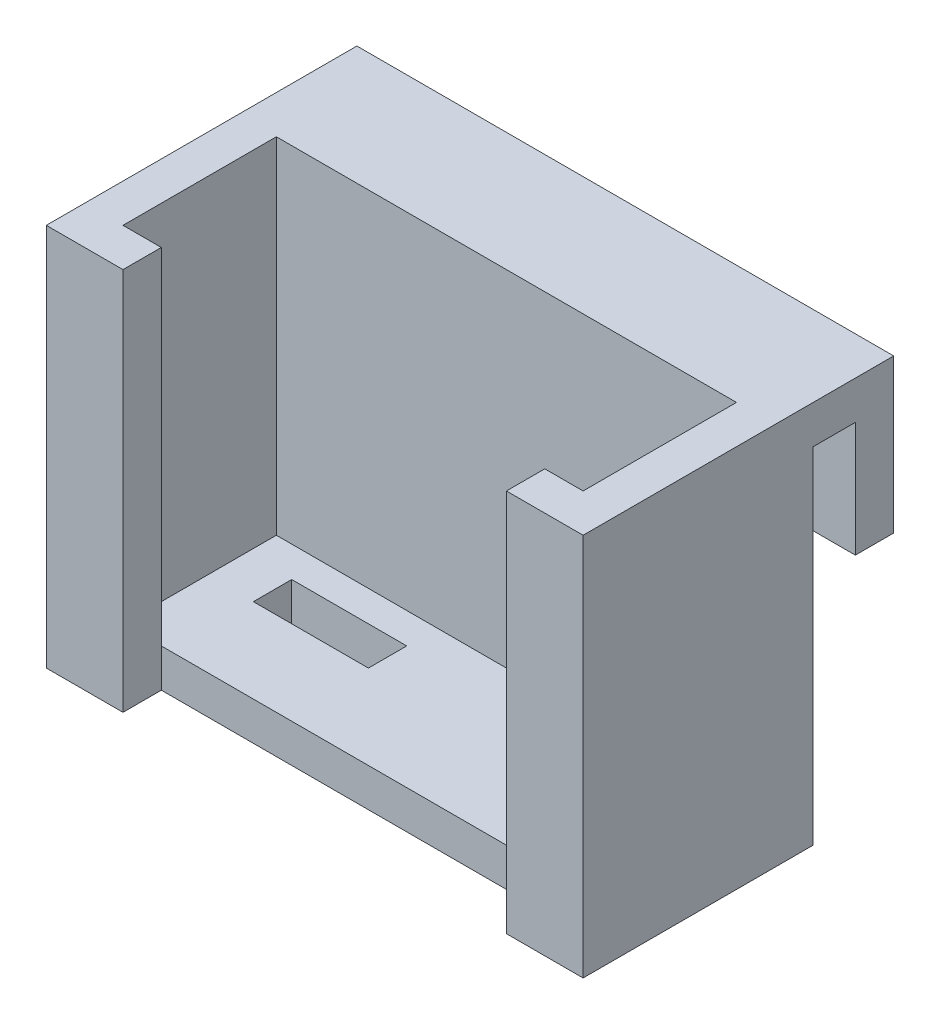
SolidWorks part; units mm, degrees
other "Markup1"
sketch "Sketch6" plane through (35, 50, 10) normal (0.115, 0.1196, 0.9861) x (0.9808, -0.1709, -0.0937)
ref_plane "Front Plane" through (0, 0, 0) normal (0, 0, 1) x (1, 0, 0)
ref_plane "Top Plane" through (0, 0, 0) normal (0, 1, 0) x (1, 0, 0)
ref_plane "Right Plane" through (0, 0, 0) normal (1, 0, 0) x (0, 0, -1)
sketch "Sketch1" plane through (0, 0, 0) normal (0, 1, 0) x (1, 0, 0)
  line L1 (30, 10) -> (-30, 10)
  line L2 (30, 10) -> (30, -10)
  line L3 (30, -10) -> (-30, -10)
  line L4 (-30, 10) -> (-30, -10)
  line L5 (30, 10) -> (-30, -10) construction
  line L6 (30, -10) -> (-30, 10) construction
  point P0 (0, 0)
  dimension "D1" = 20
  dimension "D2" = 60
extrude "Boss-Extrude1" add sketch "Sketch1" along normal blind 5
sketch "Sketch2" plane through (0, 5, 0) normal (0, 1, 0) x (1, 0, 0)
  line L0 (-30, 0) -> (-9, 0) construction
  line L1 (-30, 10) -> (-30, -10) construction
  line L2 (-9, 10) -> (-9, 1) construction
  line L3 (30, 10) -> (-30, 10) construction
  line L5 (-9, 1) -> (-24, 1)
  line L6 (-9, 1) -> (-9, 6)
  line L7 (-9, 6) -> (-24, 6)
  line L8 (-24, 1) -> (-24, 6)
  dimension "D1" = 21
  dimension "D2" = 9
  dimension "D3" = 15
  dimension "D4" = 5
extrude "Cut-Extrude1" cut sketch "Sketch2" against normal blind 5
sketch "Sketch3" plane through (0, 0, -10) normal (0, 0, -1) x (-1, 0, 0)
  line L1 (-30, 0) -> (30, 0)
  line L2 (-30, 0) -> (-30, 50)
  line L3 (-30, 50) -> (30, 50)
  line L4 (30, 0) -> (30, 50)
  dimension "D1" = 60
  dimension "D2" = 50
extrude "Boss-Extrude2" add sketch "Sketch3" along normal blind 5
sketch "Sketch4" plane through (30, 0, 0) normal (1, 0, 0) x (0, 0, -1)
  line L1 (15, 0) -> (-10, 0)
  line L2 (15, 0) -> (15, 50)
  line L3 (15, 50) -> (-10, 50)
  line L4 (-10, 0) -> (-10, 50)
  dimension "D1" = 50
  dimension "D2" = 25
extrude "Boss-Extrude3" add sketch "Sketch4" along normal blind 5
sketch "Sketch5" plane through (-30, 0, 0) normal (-1, 0, 0) x (0, 0, 1)
  line L1 (-15, 0) -> (10, 0)
  line L2 (-15, 0) -> (-15, 50)
  line L3 (-15, 50) -> (10, 50)
  line L4 (10, 0) -> (10, 50)
extrude "Boss-Extrude4" add sketch "Sketch5" along normal blind 5
sketch "Sketch7" plane through (0, 0, 10) normal (0, 0, 1) x (1, 0, 0)
  line L0 (-30, 50) -> (30, 50) construction
  line L1 (35, 0) -> (25, 0)
  line L2 (35, 0) -> (35, 50)
  line L3 (35, 50) -> (25, 50)
  line L4 (25, 0) -> (25, 50)
  dimension "D1" = 10
extrude "Boss-Extrude5" add sketch "Sketch7" along normal blind 5
sketch "Sketch8" plane through (0, 0, 10) normal (0, 0, 1) x (1, 0, 0)
  line L0 (-35, 0) -> (-35, 50) construction
  line L1 (-35, 0) -> (-25, 0)
  line L2 (-35, 0) -> (-35, 50)
  line L3 (-35, 50) -> (-25, 50)
  line L4 (-25, 0) -> (-25, 50)
  line L5 (-30, 50) -> (30, 50) construction
  dimension "D1" = 10
extrude "Boss-Extrude6" add sketch "Sketch8" along normal blind 5
sketch "Sketch9" plane through (0, 50, 0) normal (0, 1, 0) x (1, 0, 0)
  line L1 (-35, 15) -> (35, 15)
  line L2 (-35, 15) -> (-35, 20.5)
  line L3 (-35, 20.5) -> (35, 20.5)
  line L4 (35, 15) -> (35, 20.5)
  dimension "D1" = 70
  dimension "D2" = 5.5
extrude "Boss-Extrude8" add sketch "Sketch9" against normal blind 5
sketch "Sketch11" plane through (0, 0, -20.5) normal (0, 0, -1) x (-1, 0, 0)
  line L0 (35, 45) -> (35, 0) construction
  line L1 (-35, 50) -> (35, 50)
  line L2 (-35, 50) -> (-35, 30)
  line L3 (-35, 30) -> (35, 30)
  line L4 (35, 50) -> (35, 30)
  dimension "D1" = 20
extrude "Boss-Extrude9" add sketch "Sketch11" along normal blind 5
